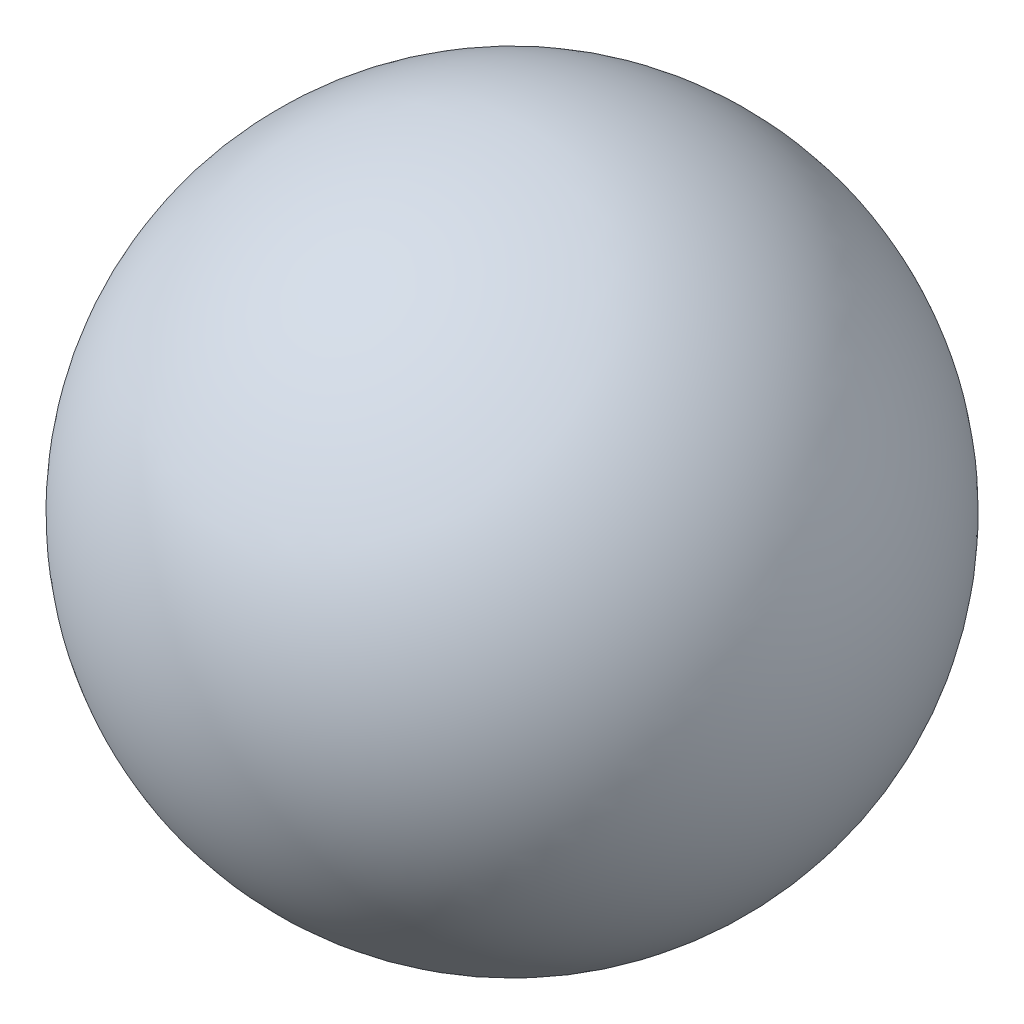
SolidWorks part; units mm, degrees
material "AISI 304"
ref_plane "Front Plane" through (0, 0, 0) normal (0, 0, 1) x (1, 0, 0)
ref_plane "Top Plane" through (0, 0, 0) normal (0, 1, 0) x (1, 0, 0)
ref_plane "Right Plane" through (0, 0, 0) normal (1, 0, 0) x (0, 0, -1)
sketch "Sketch1" plane through (0, 0, 0) normal (0, 1, 0) x (1, 0, 0)
  line L0 (0, -6.35) -> (0, 6.35)
  arc A0 (0, -6.35) -> (0, 6.35) centre (0, 0) cw
  dimension "D1" = 6.35
revolve "Revolve1" add sketch "Sketch1" angle 360 about L0
